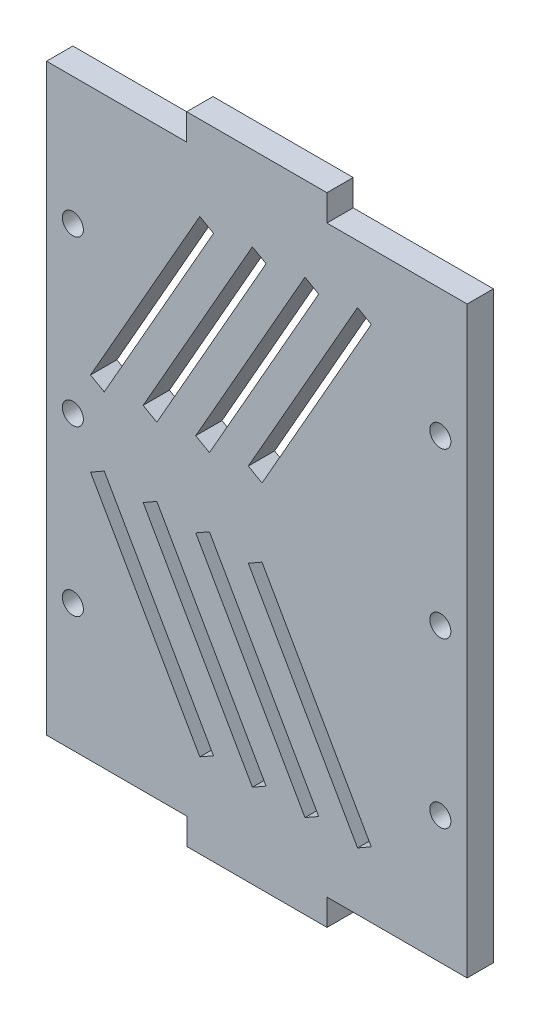
SolidWorks part; units mm, degrees
ref_plane "Alzado" through (0, 0, 0) normal (0, 0, 1) x (1, 0, 0)
ref_plane "Planta" through (0, 0, 0) normal (0, 1, 0) x (1, 0, 0)
ref_plane "Vista lateral" through (0, 0, 0) normal (1, 0, 0) x (0, 0, -1)
sketch "Croquis1" plane through (0, 0, 0) normal (0, 0, 1) x (1, 0, 0)
  line L0 (0.0183, -0.0712) -> (80, -0.0712)
  line L1 (80, -0.0712) -> (80, 110.9288)
  line L2 (80, 110.9288) -> (0.0183, 110.9288)
  line L3 (0.0183, 110.9288) -> (0.0183, -0.0712)
  line L4 (40.9893, 48.913) -> (38.3822, 47.4288)
  line L5 (59.1608, 10.9288) -> (61.7679, 12.413)
  line L6 (38.3822, 47.4288) -> (59.1608, 10.9288)
  line L7 (61.7679, 12.413) -> (40.9893, 48.913)
  line L8 (49.1608, 10.9288) -> (51.7679, 12.413)
  line L9 (51.7679, 12.413) -> (30.9893, 48.913)
  line L10 (28.3822, 47.4288) -> (49.1608, 10.9288)
  line L11 (30.9893, 48.913) -> (28.3822, 47.4288)
  line L12 (20.9893, 48.913) -> (18.3822, 47.4288)
  line L13 (39.1608, 10.9288) -> (41.7679, 12.413)
  line L14 (18.3822, 47.4288) -> (39.1608, 10.9288)
  line L15 (41.7679, 12.413) -> (20.9893, 48.913)
  line L16 (29.1608, 10.9288) -> (31.7679, 12.413)
  line L17 (10.9893, 48.913) -> (8.3822, 47.4288)
  line L18 (31.7679, 12.413) -> (10.9893, 48.913)
  line L19 (8.3822, 47.4288) -> (29.1608, 10.9288)
  line L20 (38.3822, 63.4288) -> (40.9893, 61.9446)
  line L21 (40.9893, 61.9446) -> (61.7679, 98.4446)
  line L22 (61.7679, 98.4446) -> (59.1608, 99.9288)
  line L23 (59.1608, 99.9288) -> (38.3822, 63.4288)
  line L24 (51.7679, 98.4446) -> (49.1608, 99.9288)
  line L25 (28.3822, 63.4288) -> (30.9893, 61.9446)
  line L26 (30.9893, 61.9446) -> (51.7679, 98.4446)
  line L27 (49.1608, 99.9288) -> (28.3822, 63.4288)
  line L28 (18.3822, 63.4288) -> (20.9893, 61.9446)
  line L29 (20.9893, 61.9446) -> (41.7679, 98.4446)
  line L30 (39.1608, 99.9288) -> (18.3822, 63.4288)
  line L31 (41.7679, 98.4446) -> (39.1608, 99.9288)
  line L32 (31.7679, 98.4446) -> (29.1608, 99.9288)
  line L33 (8.3822, 63.4288) -> (10.9893, 61.9446)
  line L34 (10.9893, 61.9446) -> (31.7679, 98.4446)
  line L35 (29.1608, 99.9288) -> (8.3822, 63.4288)
  dimension "D1" = 0.0183
  dimension "D2" = 8.3822
  dimension "D3" = 10.9893
  dimension "D4" = 18.3822
  dimension "D5" = 28.3822
  dimension "D6" = 29.1608
  dimension "D7" = 31.7679
  dimension "D8" = 38.3822
  dimension "D9" = 10.9288
  dimension "D10" = 12.413
  dimension "D11" = 61.9446
  dimension "D17" = 110.9288
  dimension "D18" = 80
  dimension "D19" = 0.0712
extrude "Saliente-Extruir1" add sketch "Croquis1" along normal blind 5
sketch "Croquis2" plane through (0, -0.0712, 0) normal (0, -1, 0) x (1, 0, 0)
  line L0 (0.0183, 0) -> (80, 0) construction
  line L1 (26.685, 5) -> (53.3516, 5)
  line L2 (26.685, 5) -> (26.685, 0)
  line L3 (26.685, 0) -> (53.3516, 0)
  line L4 (53.3516, 5) -> (53.3516, 0)
  line L5 (0.0183, 5) -> (0.0183, 0) construction
  dimension "D1" = 26.6667
  dimension "D2" = 26.6667
extrude "Saliente-Extruir2" add sketch "Croquis2" along normal blind 5
sketch "Croquis3" plane through (0, 110.9288, 0) normal (0, 1, 0) x (1, 0, 0)
  line L0 (80, -5) -> (0.0183, -5) construction
  line L1 (53.3333, -5) -> (26.6667, -5)
  line L2 (53.3333, -5) -> (53.3333, 0)
  line L3 (53.3333, 0) -> (26.6667, 0)
  line L4 (26.6667, -5) -> (26.6667, 0)
  line L5 (80, 0) -> (0.0183, 0) construction
  line L6 (80, -5) -> (80, 0) construction
  dimension "D1" = 26.6667
  dimension "D2" = 26.6667
extrude "Saliente-Extruir3" add sketch "Croquis3" along normal blind 5
sketch "Croquis4" plane through (0, 0, 5) normal (0, 0, 1) x (1, 0, 0)
  line L0 (74.9, 110.9288) -> (74.9, -0.0712) construction
  line L1 (80, 110.9288) -> (53.3333, 110.9288) construction
  line L2 (53.3516, -0.0712) -> (80, -0.0712) construction
  line L3 (80, -0.0712) -> (80, 110.9288) construction
  line L4 (5.0183, 110.9288) -> (5.0183, -0.0712) construction
  line L7 (26.6667, 110.9288) -> (0.0183, 110.9288) construction
  line L8 (0.0183, -0.0712) -> (26.685, -0.0712) construction
  line L9 (0.0183, 110.9288) -> (0.0183, -0.0712) construction
  circle A0 centre (74.9, 55.4288) radius 2
  circle A1 centre (74.9, 86.6788) radius 2
  circle A2 centre (74.9, 24.1788) radius 2
  circle A3 centre (5.0183, 55.4288) radius 2
  circle A4 centre (5.0183, 86.6788) radius 2
  circle A5 centre (5.0183, 24.1788) radius 2
  dimension "D1" = 4
  dimension "D2" = 4
  dimension "D3" = 4
  dimension "D7" = 4
  dimension "D8" = 4
  dimension "D9" = 4
  dimension "D4" = 31.25
  dimension "D5" = 31.25
  dimension "D6" = 5.1
  dimension "D10" = 5
  dimension "D11" = 31.25
  dimension "D12" = 31.25
extrude "Cortar-Extruir1" cut sketch "Croquis4" against normal blind 10
sketch "Croquis5" plane through (0, 0, 5) normal (0, 0, 1) x (1, 0, 0)
  line L0 (29.1608, 10.9288) -> (31.7679, 12.413) construction
  line L1 (8.3822, 47.4288) -> (29.1608, 10.9288) construction
  line L2 (31.7679, 12.413) -> (10.9893, 48.913) construction
  line L3 (10.9893, 48.913) -> (8.3822, 47.4288) construction
  line L4 (41.7679, 12.413) -> (20.9893, 48.913) construction
  line L5 (18.3822, 47.4288) -> (39.1608, 10.9288) construction
  line L6 (39.1608, 10.9288) -> (41.7679, 12.413) construction
  line L7 (20.9893, 48.913) -> (18.3822, 47.4288) construction
  line L8 (30.9893, 48.913) -> (28.3822, 47.4288) construction
  line L9 (49.1608, 10.9288) -> (51.7679, 12.413) construction
  line L10 (28.3822, 47.4288) -> (49.1608, 10.9288) construction
  line L11 (51.7679, 12.413) -> (30.9893, 48.913) construction
  line L12 (0.0183, 110.9288) -> (0.0183, -0.0712)
  line L13 (0.0183, -0.0712) -> (26.685, -0.0712)
  line L14 (26.685, -0.0712) -> (26.685, -5.0712)
  line L15 (26.685, -5.0712) -> (53.3516, -5.0712)
  line L16 (53.3516, -5.0712) -> (53.3516, -0.0712)
  line L17 (53.3516, -0.0712) -> (80, -0.0712)
  line L18 (80, -0.0712) -> (80, 110.9288)
  line L19 (80, 110.9288) -> (53.3333, 110.9288)
  line L20 (53.3333, 110.9288) -> (53.3333, 115.9288)
  line L21 (53.3333, 115.9288) -> (26.6667, 115.9288)
  line L22 (26.6667, 115.9288) -> (26.6667, 110.9288)
  line L23 (26.6667, 110.9288) -> (0.0183, 110.9288)
  line L24 (0.0183, 110.9288) -> (0.0183, -0.0712)
  line L25 (0.0183, -0.0712) -> (26.685, -0.0712)
  line L26 (26.685, -0.0712) -> (26.685, -5.0712)
  line L27 (26.685, -5.0712) -> (53.3516, -5.0712)
  line L28 (53.3516, -5.0712) -> (53.3516, -0.0712)
  line L29 (53.3516, -0.0712) -> (80, -0.0712)
  line L30 (80, -0.0712) -> (80, 110.9288)
  line L31 (80, 110.9288) -> (53.3333, 110.9288)
  line L32 (53.3333, 110.9288) -> (53.3333, 115.9288)
  line L33 (53.3333, 115.9288) -> (26.6667, 115.9288)
  line L34 (26.6667, 115.9288) -> (26.6667, 110.9288)
  line L35 (26.6667, 110.9288) -> (0.0183, 110.9288)
  line L36 (38.3822, 47.4288) -> (59.1608, 10.9288) construction
  line L37 (61.7679, 12.413) -> (40.9893, 48.913) construction
  line L38 (59.1608, 10.9288) -> (61.7679, 12.413) construction
  line L39 (40.9893, 48.913) -> (38.3822, 47.4288) construction
  line L40 (31.7679, 98.4446) -> (29.1608, 99.9288) construction
  line L41 (10.9893, 61.9446) -> (31.7679, 98.4446) construction
  line L42 (29.1608, 99.9288) -> (8.3822, 63.4288) construction
  line L43 (8.3822, 63.4288) -> (10.9893, 61.9446) construction
  line L44 (18.3822, 63.4288) -> (20.9893, 61.9446) construction
  line L45 (20.9893, 61.9446) -> (41.7679, 98.4446) construction
  line L46 (41.7679, 98.4446) -> (39.1608, 99.9288) construction
  line L47 (39.1608, 99.9288) -> (18.3822, 63.4288) construction
  line L48 (51.7679, 98.4446) -> (49.1608, 99.9288) construction
  line L49 (30.9893, 61.9446) -> (51.7679, 98.4446) construction
  line L50 (49.1608, 99.9288) -> (28.3822, 63.4288) construction
  line L51 (28.3822, 63.4288) -> (30.9893, 61.9446) construction
  line L52 (38.3822, 63.4288) -> (40.9893, 61.9446) construction
  line L53 (61.7679, 98.4446) -> (59.1608, 99.9288) construction
  line L54 (40.9893, 61.9446) -> (61.7679, 98.4446) construction
  line L55 (59.1608, 99.9288) -> (38.3822, 63.4288) construction
  line L56 (29.1608, 10.9288) -> (31.7679, 12.413)
  line L57 (8.3822, 47.4288) -> (29.1608, 10.9288)
  line L58 (31.7679, 12.413) -> (10.9893, 48.913)
  line L59 (10.9893, 48.913) -> (8.3822, 47.4288)
  line L60 (41.7679, 12.413) -> (20.9893, 48.913)
  line L61 (18.3822, 47.4288) -> (39.1608, 10.9288)
  line L62 (39.1608, 10.9288) -> (41.7679, 12.413)
  line L63 (20.9893, 48.913) -> (18.3822, 47.4288)
  line L64 (30.9893, 48.913) -> (28.3822, 47.4288)
  line L65 (49.1608, 10.9288) -> (51.7679, 12.413)
  line L66 (28.3822, 47.4288) -> (49.1608, 10.9288)
  line L67 (51.7679, 12.413) -> (30.9893, 48.913)
  line L68 (38.3822, 47.4288) -> (59.1608, 10.9288)
  line L69 (61.7679, 12.413) -> (40.9893, 48.913)
  line L70 (59.1608, 10.9288) -> (61.7679, 12.413)
  line L71 (40.9893, 48.913) -> (38.3822, 47.4288)
  line L72 (31.7679, 98.4446) -> (29.1608, 99.9288)
  line L73 (10.9893, 61.9446) -> (31.7679, 98.4446)
  line L74 (29.1608, 99.9288) -> (8.3822, 63.4288)
  line L75 (8.3822, 63.4288) -> (10.9893, 61.9446)
  line L76 (18.3822, 63.4288) -> (20.9893, 61.9446)
  line L77 (20.9893, 61.9446) -> (41.7679, 98.4446)
  line L78 (41.7679, 98.4446) -> (39.1608, 99.9288)
  line L79 (39.1608, 99.9288) -> (18.3822, 63.4288)
  line L80 (51.7679, 98.4446) -> (49.1608, 99.9288)
  line L81 (30.9893, 61.9446) -> (51.7679, 98.4446)
  line L82 (49.1608, 99.9288) -> (28.3822, 63.4288)
  line L83 (28.3822, 63.4288) -> (30.9893, 61.9446)
  line L84 (38.3822, 63.4288) -> (40.9893, 61.9446)
  line L85 (61.7679, 98.4446) -> (59.1608, 99.9288)
  line L86 (40.9893, 61.9446) -> (61.7679, 98.4446)
  line L87 (59.1608, 99.9288) -> (38.3822, 63.4288)
  circle A0 centre (74.9, 24.1788) radius 2 construction
  circle A1 centre (74.9, 55.4288) radius 2 construction
  circle A2 centre (74.9, 86.6788) radius 2 construction
  circle A3 centre (5.0183, 86.6788) radius 2 construction
  circle A4 centre (5.0183, 55.4288) radius 2 construction
  circle A5 centre (5.0183, 24.1788) radius 2 construction
  circle A6 centre (74.9, 24.1788) radius 2
  circle A7 centre (74.9, 55.4288) radius 2
  circle A8 centre (74.9, 86.6788) radius 2
  circle A9 centre (5.0183, 86.6788) radius 2
  circle A10 centre (5.0183, 55.4288) radius 2
  circle A11 centre (5.0183, 24.1788) radius 2
  dimension "D1" = 0
